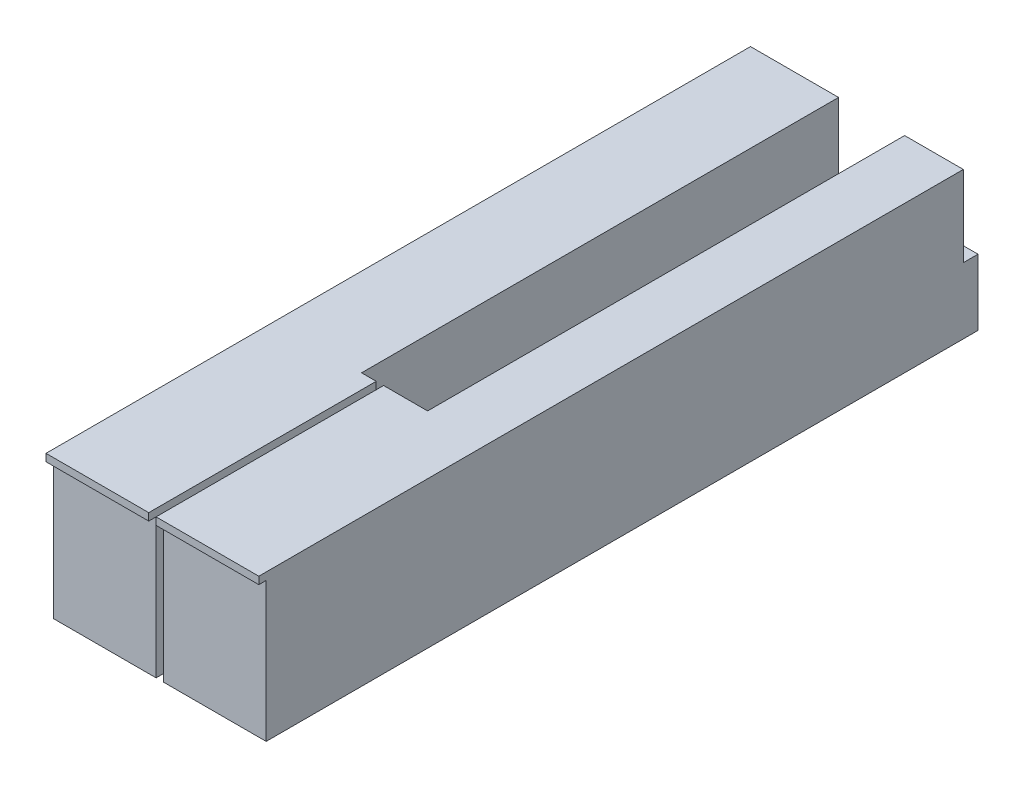
SolidWorks part; units mm, degrees
material "PE High Density Film"
ref_plane "Front Plane" through (0, 0, 0) normal (0, 0, 1) x (1, 0, 0)
ref_plane "Top Plane" through (0, 0, 0) normal (0, 1, 0) x (1, 0, 0)
ref_plane "Right Plane" through (0, 0, 0) normal (1, 0, 0) x (0, 0, -1)
sketch "Sketch1" plane through (0, 0, 0) normal (0, 1, 0) x (1, 0, 0)
  line L0 (0, 0) -> (0, 152.4)
  line L1 (0, 152.4) -> (-12.7, 152.4)
  line L2 (-12.7, 152.4) -> (-12.7, 49.2125)
  line L3 (-12.7, 49.2125) -> (-22.225, 49.2125)
  line L4 (-22.225, 49.2125) -> (-22.225, 0)
  line L5 (-22.225, 0) -> (0, 0)
  line L12 (-23.8125, 0) -> (-46.0375, 0)
  line L13 (-46.0375, 0) -> (-46.0375, 152.4)
  line L14 (-46.0375, 152.4) -> (-26.9875, 152.4)
  line L15 (-26.9875, 152.4) -> (-26.9875, 49.2125)
  line L16 (-26.9875, 49.2125) -> (-23.8125, 49.2125)
  line L17 (-23.8125, 49.2125) -> (-23.8125, 0)
  dimension "D1" = 49.2125
  dimension "D2" = 1.5875
  dimension "D3" = 22.225
  dimension "D4" = 152.4
  dimension "D5" = 9.525
  dimension "D6" = 14.2875
extrude "Boss-Extrude1" add sketch "Sketch1" along normal blind 31.75
sketch "Sketch2" plane through (0, 0, 0) normal (1, 0, 0) x (0, 0, -1)
  line L0 (0, 31.75) -> (152.4, 31.75) construction
  line L1 (0, 0) -> (1.5875, 0)
  line L2 (0, 0) -> (0, 30.1625)
  line L3 (0, 30.1625) -> (1.5875, 30.1625)
  line L4 (1.5875, 0) -> (1.5875, 30.1625)
  dimension "D1" = 1.5875
  dimension "D2" = 1.5875
extrude "Cut-Extrude1" cut sketch "Sketch2" against normal through all
sketch "Sketch3" plane through (0, 0, 0) normal (1, 0, 0) x (0, 0, -1)
  line L1 (152.4, 0) -> (155.575, 0)
  line L2 (152.4, 0) -> (152.4, 14.2875)
  line L3 (152.4, 14.2875) -> (155.575, 14.2875)
  line L4 (155.575, 0) -> (155.575, 14.2875)
  dimension "D1" = 14.2875
  dimension "D2" = 3.175
extrude "Boss-Extrude2" add sketch "Sketch3" against normal up to surface (46.0375 mm away) up to face at (-46.0375, 20.6375, -51.3292)
